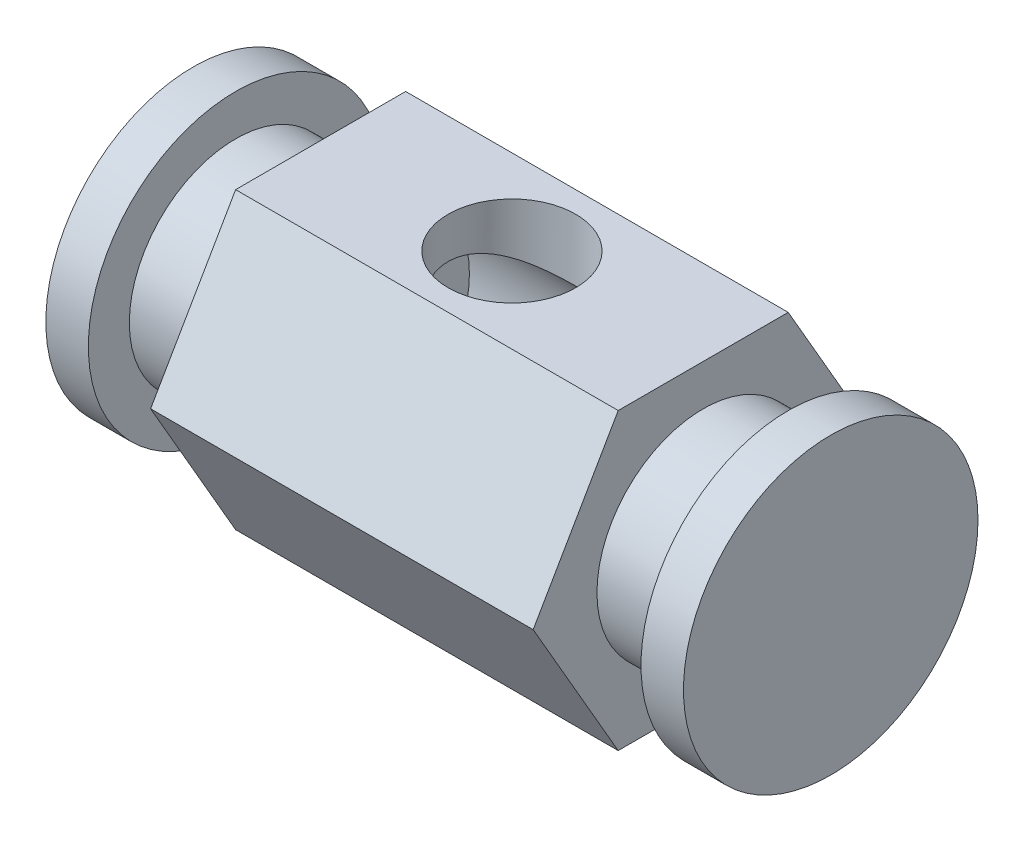
SolidWorks part; units mm, degrees
ref_plane "Front Plane" through (0, 0, 0) normal (0, 0, 1) x (1, 0, 0)
ref_plane "Top Plane" through (0, 0, 0) normal (0, 1, 0) x (1, 0, 0)
ref_plane "Right Plane" through (0, 0, 0) normal (1, 0, 0) x (0, 0, -1)
sketch "Sketch1" plane through (0, 0, 0) normal (1, 0, 0) x (0, 0, -1)
  line L1 (10, 17.3205) -> (-10, 17.3205)
  line L2 (-10, 17.3205) -> (-20, 0)
  line L3 (-20, 0) -> (-10, -17.3205)
  line L4 (-10, -17.3205) -> (10, -17.3205)
  line L5 (10, -17.3205) -> (20, 0)
  line L6 (20, 0) -> (10, 17.3205)
  circle A0 centre (0, 0) radius 17.3205 construction
  circle A1 centre (0, 0) radius 12.5
  dimension "D2" = 25
  dimension "D1" = 40
extrude "Boss-Extrude1" add sketch "Sketch1" along normal mid plane 45
sketch "Sketch2" plane through (0, 0, 0) normal (0, 1, 0) x (1, 0, 0)
  circle A0 centre (0, 0) radius 7.5
  dimension "D1" = 15
extrude "Cut-Extrude2" cut sketch "Sketch2" against normal through all both and the other way through all contours A0
sketch "Sketch3" plane through (22.5, 0, 0) normal (1, 0, 0) x (0, 0, -1)
  circle A0 centre (0, 0) radius 12.5
  circle A2 centre (0, 0) radius 12.5 construction
extrude "Boss-Extrude2" add sketch "Sketch3" along normal blind 10 and the other way blind 5
sketch "Sketch4" plane through (32.5, 0, 0) normal (1, 0, 0) x (0, 0, -1)
  line L0 (10, -17.3205) -> (20, 0) construction
  circle A0 centre (0, 0) radius 17.3205
extrude "Boss-Extrude3" add sketch "Sketch4" along normal blind 5
mirror "Mirror3" about plane through (0, 0, 0) normal (1, 0, 0) of "Boss-Extrude2", "Boss-Extrude3"
